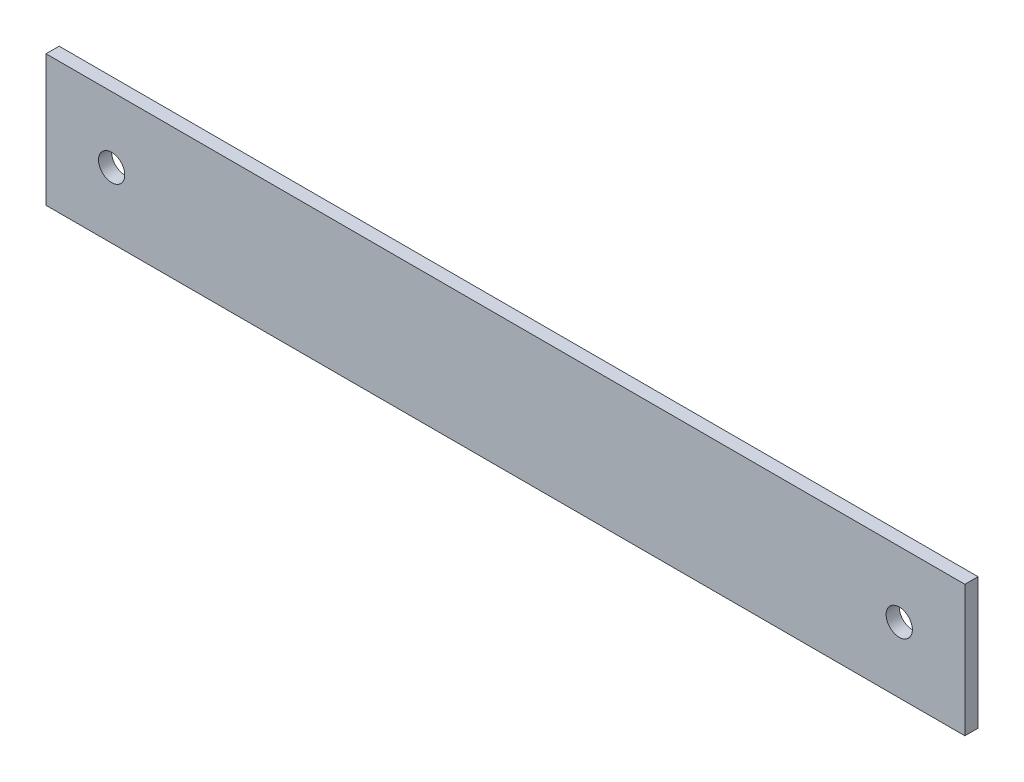
SolidWorks part; units mm, degrees
material "7075-T6 (SN)"
ref_plane "Front Plane" through (0, 0, 0) normal (0, 0, 1) x (1, 0, 0)
ref_plane "Top Plane" through (0, 0, 0) normal (0, 1, 0) x (1, 0, 0)
ref_plane "Right Plane" through (0, 0, 0) normal (1, 0, 0) x (0, 0, -1)
sketch "Sketch1" plane through (0, 0, 0) normal (0, 0, 1) x (1, 0, 0)
  line L1 (-70, -10) -> (70, -10)
  line L2 (-70, -10) -> (-70, 10)
  line L3 (-70, 10) -> (70, 10)
  line L4 (70, -10) -> (70, 10)
  line L5 (-70, -10) -> (70, 10) construction
  line L6 (-70, 10) -> (70, -10) construction
  point P0 (0, 0)
  dimension "D1" = 20
  dimension "D2" = 140
extrude "Boss-Extrude1" add sketch "Sketch1" along normal blind 2
sketch "Sketch2" plane through (0, 0, 2) normal (0, 0, 1) x (1, 0, 0)
  line L0 (-77.6256, 0) -> (87.5667, 0) construction
  line L1 (60, 15.7225) -> (60, -15.6799) construction
  line L2 (-60, 19.153) -> (-60, -16.7355) construction
  line L3 (-70, 10) -> (-70, -10) construction
  line L4 (70, -10) -> (70, 10) construction
  circle A0 centre (-60, 0) radius 2
  circle A1 centre (60, 0) radius 2
  dimension "D3" = 4
  dimension "D4" = 4
  dimension "D1" = 10
  dimension "D2" = 10
extrude "Cut-Extrude1" cut sketch "Sketch2" against normal through all
